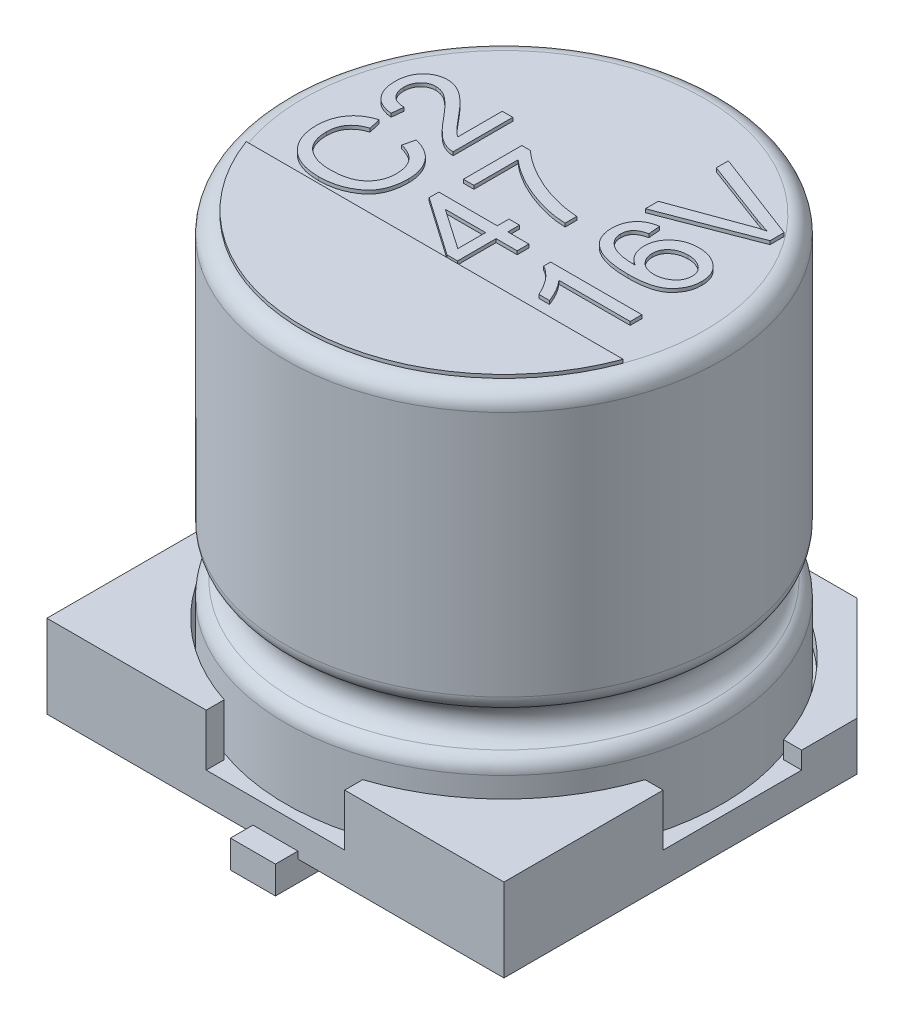
SolidWorks part; units mm, degrees
ref_plane "Plan de face" through (0, 0, 0) normal (0, 0, 1) x (1, 0, 0)
ref_plane "Plan de dessus" through (0, 0, 0) normal (0, 1, 0) x (1, 0, 0)
ref_plane "Plan de droite" through (0, 0, 0) normal (1, 0, 0) x (0, 0, -1)
sketch "Esquisse1" plane through (0, 0, 0) normal (0, 1, 0) x (1, 0, 0)
  line L1 (-3.3, -3.3) -> (3.3, -3.3)
  line L2 (-3.3, -3.3) -> (-3.3, 3.3)
  line L3 (-3.3, 3.3) -> (3.3, 3.3)
  line L4 (3.3, -3.3) -> (3.3, 3.3)
  line L5 (-3.3, -3.3) -> (3.3, 3.3) construction
  line L6 (-3.3, 3.3) -> (3.3, -3.3) construction
  point P0 (0, 0)
  dimension "D1" = 6.6
extrude "Boss.-Extru.1" add sketch "Esquisse1" along normal blind 1.2
sketch "Esquisse2" plane through (0, 1.2, 0) normal (0, 1, 0) x (1, 0, 0)
  line L0 (-3.3, 3.3) -> (-3.3, -3.3) construction
  line L1 (3.3, -1) -> (-3.3, -1)
  line L2 (3.3, -1) -> (3.3, 1)
  line L3 (3.3, 1) -> (-3.3, 1)
  line L4 (-3.3, -1) -> (-3.3, 1)
  line L5 (3.3, -1) -> (-3.3, 1) construction
  line L6 (3.3, 1) -> (-3.3, -1) construction
  line L7 (3.3, 3.3) -> (-3.3, 3.3) construction
  line L8 (-1, -3.3) -> (1, -3.3)
  line L9 (-1, -3.3) -> (-1, 3.3)
  line L10 (-1, 3.3) -> (1, 3.3)
  line L11 (1, -3.3) -> (1, 3.3)
  line L12 (-1, -3.3) -> (1, 3.3) construction
  line L13 (-1, 3.3) -> (1, -3.3) construction
  circle A0 centre (0, 0) radius 3.2
  line M1 (3.3, -3.3) -> (3.3, 3.3)
  line M2 (3.3, 3.3) -> (-3.3, 3.3)
  line M3 (-3.3, 3.3) -> (-3.3, -3.3)
  line M4 (-3.3, -3.3) -> (3.3, -3.3)
  dimension "D2" = 6.4
  dimension "D1" = 2
extrude "Enlèv. mat.-Extru.1" cut sketch "Esquisse2" against normal blind 0.75 contours A0 L3 L1 M3 | A0 L11 L9 M2 | A0 L1 L3 M1 | A0 L9 L11 M4
sketch "Esquisse3" plane through (0, 1.2, 0) normal (0, 1, 0) x (1, 0, 0)
  line L1 (-3.3, 0) -> (3.3, 0)
  line L2 (-3.3, 0) -> (-3.3, 3.3)
  line L3 (-3.3, 3.3) -> (3.3, 3.3)
  line L4 (3.3, 0) -> (3.3, 3.3)
extrude "Enlèv. mat.-Extru.2" cut sketch "Esquisse3" against normal blind 0.5
chamfer "Chanfrein1" distance 1.5 angle 45 2 edges at (3.3, 0.35, -3.3) (-3.3, 0.35, -3.3)
sketch "Esquisse4" plane through (0, 0, 0) normal (1, 0, 0) x (0, 0, -1)
  line L0 (-1, 0.45) -> (1, 0.45) construction
  line L1 (0, 0.45) -> (0, 6.25) construction
  line L2 (0, 6.25) -> (-2.9, 6.25)
  line L3 (0, 0.45) -> (-3.15, 0.45)
  line L4 (-3.15, 0.45) -> (-3.15, 1.4601)
  line L5 (-3.15, 6) -> (-3.15, 2.4399)
  line L6 (0, 0.45) -> (0, 6.25)
  arc A0 (-3.15, 1.4601) -> (-3.0136, 1.6828) centre (-2.9, 1.4601) cw
  arc A1 (-3.15, 2.4399) -> (-3.0136, 2.2172) centre (-2.9, 2.4399) ccw
  arc A2 (-3.0136, 1.6828) -> (-3.0136, 2.2172) centre (-3.15, 1.95) ccw
  arc A3 (-2.9, 6.25) -> (-3.15, 6) centre (-2.9, 6) ccw
  dimension "D1" = 0.25
  dimension "D3" = 0.3
  dimension "D5" = 0.25
  dimension "D2" = 5.8
  dimension "D4" = 6.3
  dimension "D6" = 1.5
revolve "Révolution1" add sketch "Esquisse4" angle 360 about L1
sketch "Esquisse5" plane through (0, 0, 0) normal (0, -1, 0) x (1, 0, 0)
  line L0 (-3.3, 3.3) -> (3.3, 3.3) construction
  line L1 (-0.325, 3.625) -> (0.325, 3.625)
  line L2 (-0.325, 3.625) -> (-0.325, 2.975)
  line L3 (-0.325, 2.975) -> (0.325, 2.975)
  line L4 (0.325, 3.625) -> (0.325, 2.975)
  line L5 (-0.325, 3.625) -> (0.325, 2.975) construction
  line L6 (-0.325, 2.975) -> (0.325, 3.625) construction
  line L7 (1.8, -3.3) -> (-1.8, -3.3) construction
  line L8 (-0.325, -3.625) -> (0.325, -3.625)
  line L9 (-0.325, -3.625) -> (-0.325, -2.975)
  line L10 (-0.325, -2.975) -> (0.325, -2.975)
  line L11 (0.325, -3.625) -> (0.325, -2.975)
  line L12 (-0.325, -3.625) -> (0.325, -2.975) construction
  line L13 (-0.325, -2.975) -> (0.325, -3.625) construction
  point P0 (0, 3.3)
  point P7 (0, -3.3)
  dimension "D1" = 0.65
extrude "Boss.-Extru.2" add sketch "Esquisse5" along normal blind 0.3 and the other way blind 0.1 separate body
sketch "Esquisse6" plane through (0, 0, 0) normal (0, -1, 0) x (1, 0, 0)
  line L1 (-2, -2) -> (2, -2) construction
  line L2 (-2, -2) -> (-2, 2) construction
  line L3 (-2, 2) -> (2, 2) construction
  line L4 (2, -2) -> (2, 2) construction
  line L5 (-2, -2) -> (2, 2) construction
  line L6 (-2, 2) -> (2, -2) construction
  circle A0 centre (-2, 2) radius 0.5
  circle A1 centre (2, 2) radius 0.5
  circle A2 centre (2, -2) radius 0.5
  circle A3 centre (-2, -2) radius 0.5
  point P0 (0, 0)
  dimension "D2" = 1
  dimension "D1" = 4
extrude "Boss.-Extru.3" add sketch "Esquisse6" along normal blind 0.3
sketch "Esquisse7" plane through (0, 6.25, 0) normal (0, 1, 0) x (1, 0, 0)
  line L0 (-2.7221, -1) -> (2.7221, -1)
  line L2 (0.6, 1.4825) -> (0.6, -1) construction
  line L3 (2.3, 1.4825) -> (2.3, -1) construction
  line L4 (-1.1007, 1.7727) -> (-1.1007, -1) construction
  circle A0 centre (0, 0) radius 2.9 construction
  circle A3 centre (0, 0) radius 2.9
  arc A4 (-2.7221, -1) -> (2.7221, -1) centre (0, 0) ccw
  text T1 "47" font "Arial" height 1.3
  text T2 "16V" font "Arial" height 1.3
  text T3 "C2" font "Arial" height 1.3
  dimension "D1" = 1
  dimension "D2" = 1.7007
  dimension "D3" = 1.1007
  dimension "D4" = 1.7
  dimension "D5" = 0
extrude "Boss.-Extru.4" add sketch "Esquisse7" along normal blind 0.05 separate body
